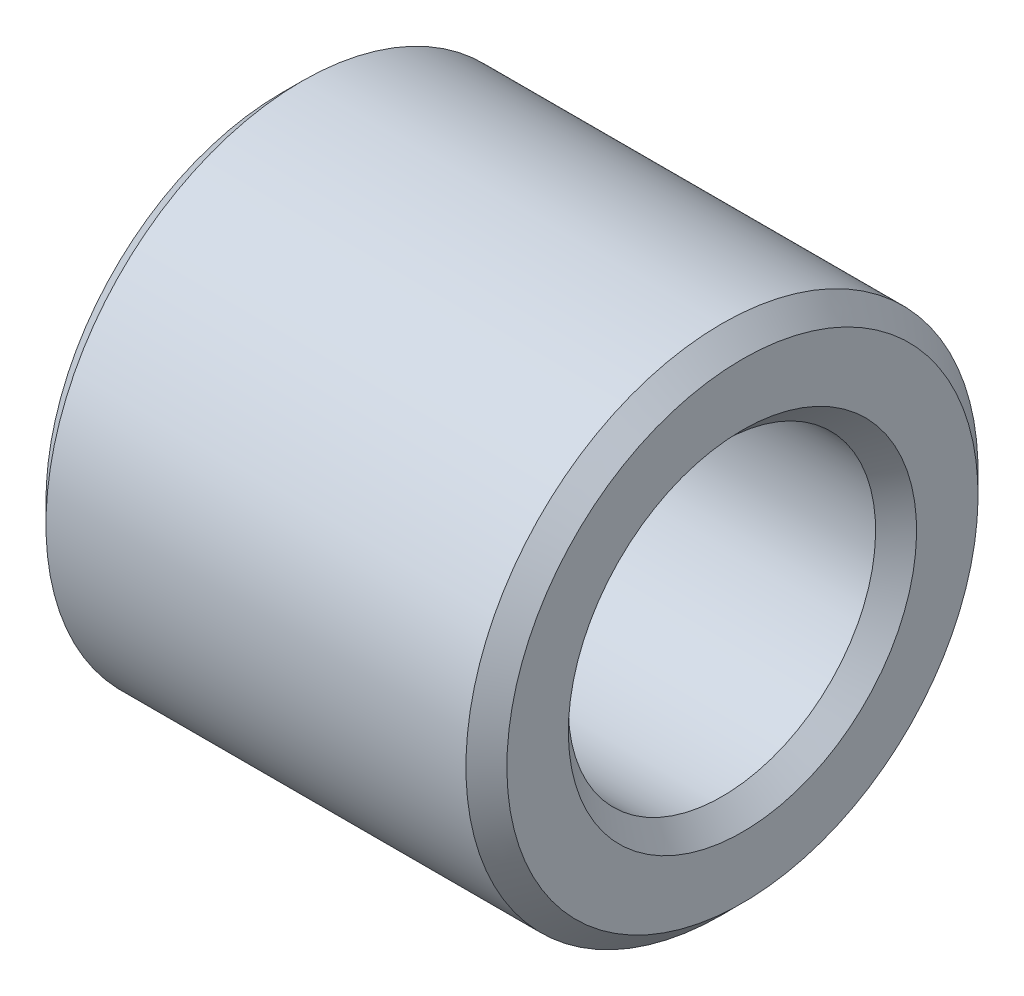
SolidWorks part; units mm, degrees
material "AISI 304"
ref_plane "正面" through (0, 0, 0) normal (0, 0, 1) x (1, 0, 0)
ref_plane "平面" through (0, 0, 0) normal (0, 1, 0) x (1, 0, 0)
ref_plane "右側面" through (0, 0, 0) normal (1, 0, 0) x (0, 0, -1)
ref_plane "Plane1" through (0, 0, 0) normal (0, 0, 1) x (1, 0, 0)
sketch "Sketch1" plane through (0, 0, 0) normal (0, 0, 1) x (1, 0, 0)
  line L0 (0, -1.7) -> (0, -2.3)
  line L1 (0, -2.3) -> (0.2, -2.5)
  line L2 (0.2, -2.5) -> (4.3, -2.5)
  line L3 (4.3, -2.5) -> (4.5, -2.3)
  line L4 (4.5, -2.3) -> (4.5, -1.7)
  line L5 (4.5, -1.7) -> (4.3, -1.5)
  line L6 (4.3, -1.5) -> (0.2, -1.5)
  line L7 (0.2, -1.5) -> (0, -1.7)
  line L8 (-3, 0) -> (3, 0) construction
  dimension "D1" = 2.5
  dimension "D2" = 1.5
  dimension "D3" = 0.6
revolve "Revolve1" add sketch "Sketch1" angle 360 about L8
